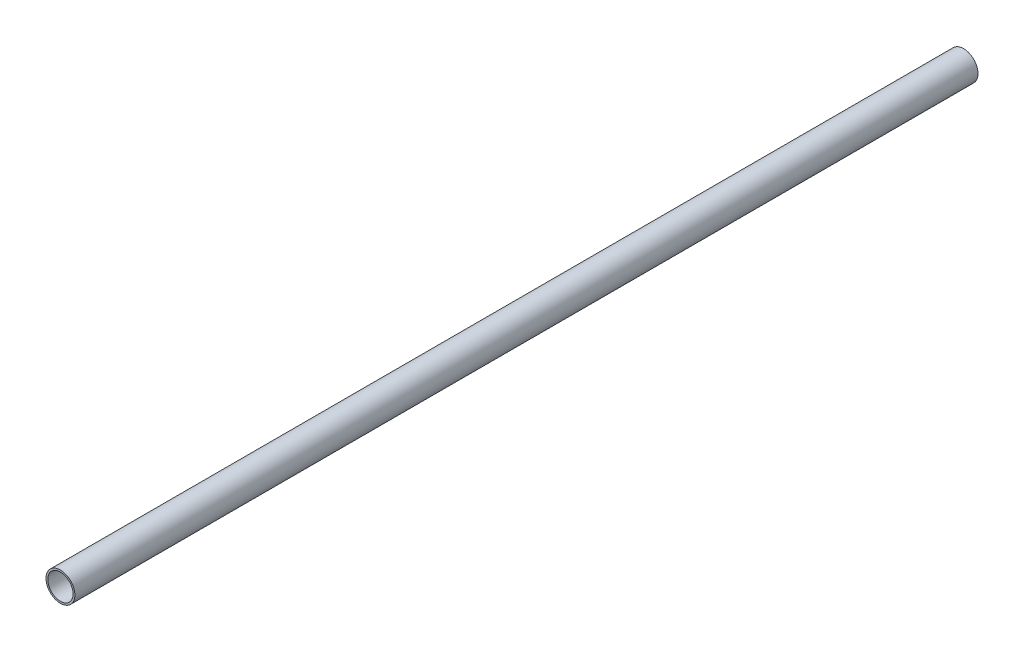
SolidWorks part; units mm, degrees
material "carbon fiber"
ref_plane "Front Plane" through (0, 0, 0) normal (0, 0, 1) x (1, 0, 0)
ref_plane "Top Plane" through (0, 0, 0) normal (0, 1, 0) x (1, 0, 0)
ref_plane "Right Plane" through (0, 0, 0) normal (1, 0, 0) x (0, 0, -1)
sketch "Эскиз1" plane through (0, 0, 0) normal (0, 0, 1) x (1, 0, 0)
  circle A0 centre (0, 0) radius 8
  circle A1 centre (0, 0) radius 7
  dimension "D1" = 16
  dimension "D2" = 1
extrude "Бобышка-Вытянуть1" add sketch "Эскиз1" along normal mid plane 500
